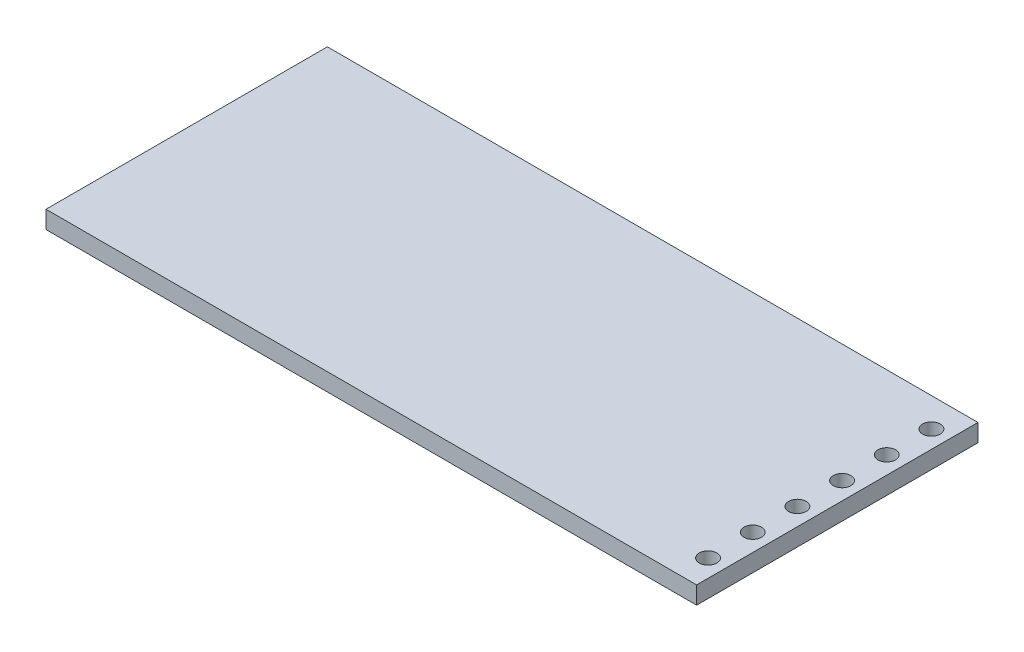
SolidWorks part; units mm, degrees
ref_plane "Front Plane" through (0, 0, 0) normal (0, 0, 1) x (1, 0, 0)
ref_plane "Top Plane" through (0, 0, 0) normal (0, 1, 0) x (1, 0, 0)
ref_plane "Right Plane" through (0, 0, 0) normal (1, 0, 0) x (0, 0, -1)
sketch "Sketch1" plane through (0, 0, 0) normal (0, 1, 0) x (1, 0, 0)
  line L1 (-18.5, 8) -> (18.5, 8)
  line L2 (-18.5, 8) -> (-18.5, -8)
  line L3 (-18.5, -8) -> (18.5, -8)
  line L4 (18.5, 8) -> (18.5, -8)
  line L5 (-18.5, 8) -> (18.5, -8) construction
  line L6 (-18.5, -8) -> (18.5, 8) construction
  point P0 (0, 0)
  dimension "D1" = 37
  dimension "D2" = 16
extrude "Boss-Extrude1" add sketch "Sketch1" along normal blind 1
sketch "Sketch2" plane through (0, 1, 0) normal (0, 1, 0) x (1, 0, 0)
  line L0 (-18.5, -8) -> (18.5, -8) construction
  line L2 (18.5, -8) -> (18.5, 8) construction
  circle A0 centre (17.5, -6.35) radius 0.5
  circle A1 centre (17.5, -3.81) radius 0.5
  circle A2 centre (17.5, -1.27) radius 0.5
  circle A3 centre (17.5, 1.27) radius 0.5
  circle A4 centre (17.5, 3.81) radius 0.5
  circle A5 centre (17.5, 6.35) radius 0.5
  dimension "D1" = 1
  dimension "D3" = 1.65
  dimension "D4" = 1
  dimension "D5" = 2.54
  dimension "D2" = 6
extrude "Cut-Extrude1" cut sketch "Sketch2" against normal blind 10
